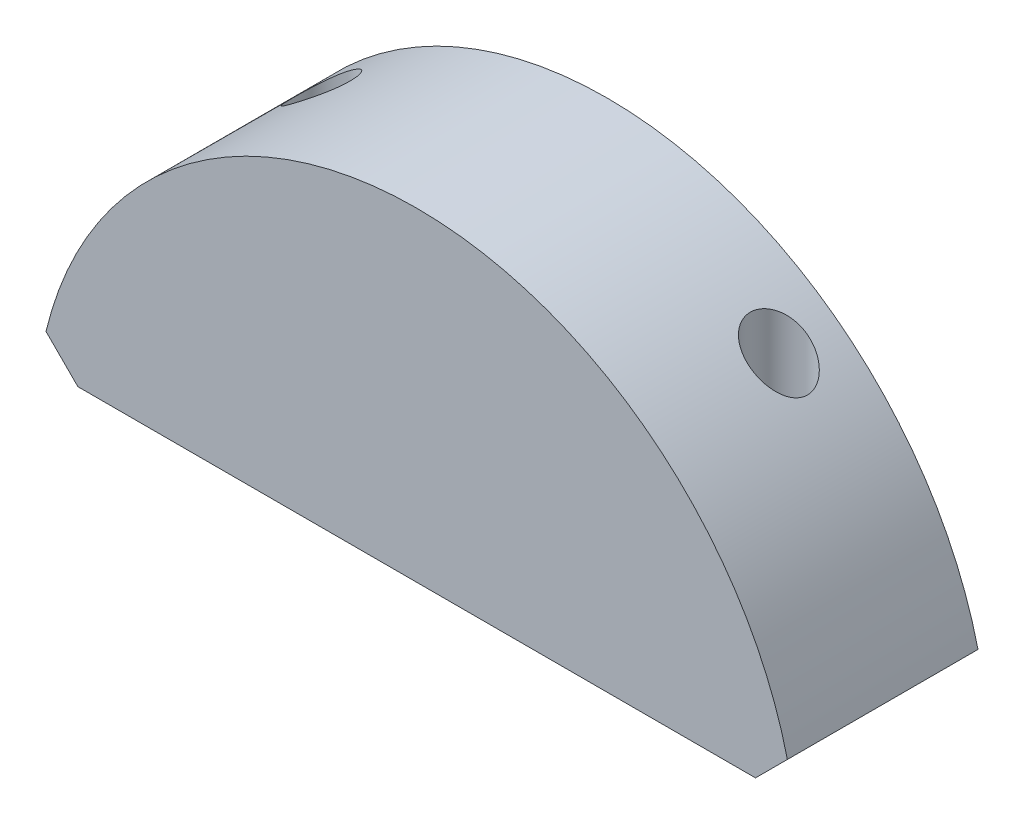
SolidWorks part; units mm, degrees
ref_plane "Plan de face" through (0, 0, 0) normal (0, 0, 1) x (1, 0, 0)
ref_plane "Plan de dessus" through (0, 0, 0) normal (0, 1, 0) x (1, 0, 0)
ref_plane "Plan de droite" through (0, 0, 0) normal (1, 0, 0) x (0, 0, -1)
sketch "Esquisse1" plane through (0, 0, 0) normal (0, 0, 1) x (1, 0, 0)
  line L0 (0, 0) -> (0, 9.1872) construction
  line L1 (17.7737, 3) -> (-17.7737, 3)
  line L2 (19.4465, 4.6728) -> (17.7737, 3)
  line L4 (-19.4465, 4.6728) -> (-17.7737, 3)
  arc A0 (19.4465, 4.6728) -> (-19.4465, 4.6728) centre (0, 0) ccw
extrude "Extrusion1" add sketch "Esquisse1" along normal blind 10
sketch "Esquisse2" plane through (0, 3, 0) normal (0, -1, 0) x (1, 0, 0)
  line L0 (0, 0) -> (0, 3) construction
  line L1 (-17.7737, 0) -> (17.7737, 0) construction
  line L2 (0, 3) -> (-12, 3) construction
  circle A0 centre (-12, 3) radius 1.5
  circle A1 centre (12, 3) radius 1.5
extrude "Extrusion2" cut sketch "Esquisse2" against normal through all
